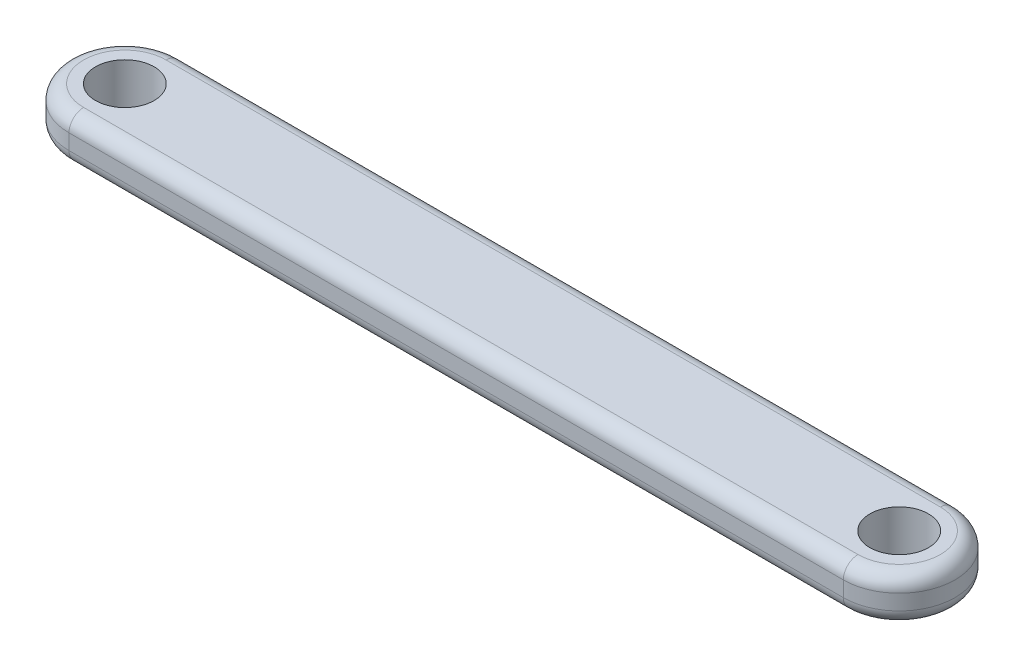
SolidWorks part; units mm, degrees
material "PLA"
ref_plane "Front Plane" through (0, 0, 0) normal (0, 0, 1) x (1, 0, 0)
ref_plane "Top Plane" through (0, 0, 0) normal (0, 1, 0) x (1, 0, 0)
ref_plane "Right Plane" through (0, 0, 0) normal (1, 0, 0) x (0, 0, -1)
sketch "Sketch1" plane through (0, 0, 0) normal (0, 1, 0) x (1, 0, 0)
  line L2 (-26.4189, 0) -> (26.4189, 0) construction
  line L7 (-26.4189, 3.81) -> (26.4189, 3.81)
  line L8 (26.4189, -3.81) -> (-26.4189, -3.81)
  circle A0 centre (-26.4189, 0) radius 2
  circle A1 centre (26.4189, 0) radius 2
  arc A4 (-26.4189, 3.81) -> (-26.4189, -3.81) centre (-26.4189, 0) ccw
  arc A7 (26.4189, -3.81) -> (26.4189, 3.81) centre (26.4189, 0) ccw
  point P0 (0, 0)
  dimension "D2" = 4
  dimension "D3" = 3.81
  dimension "D1" = 52.8377
extrude "Boss-Extrude1" add sketch "Sketch1" along normal mid plane 3.048
fillet "Fillet1" radius 1 8 edges at (-30.2289, -1.524, 0) (30.2289, -1.524, 0) (-30.2289, 1.524, 0) (30.2289, 1.524, 0) (0, -1.524, -3.81) (0, 1.524, -3.81) (0, -1.524, 3.81) (0, 1.524, 3.81)
